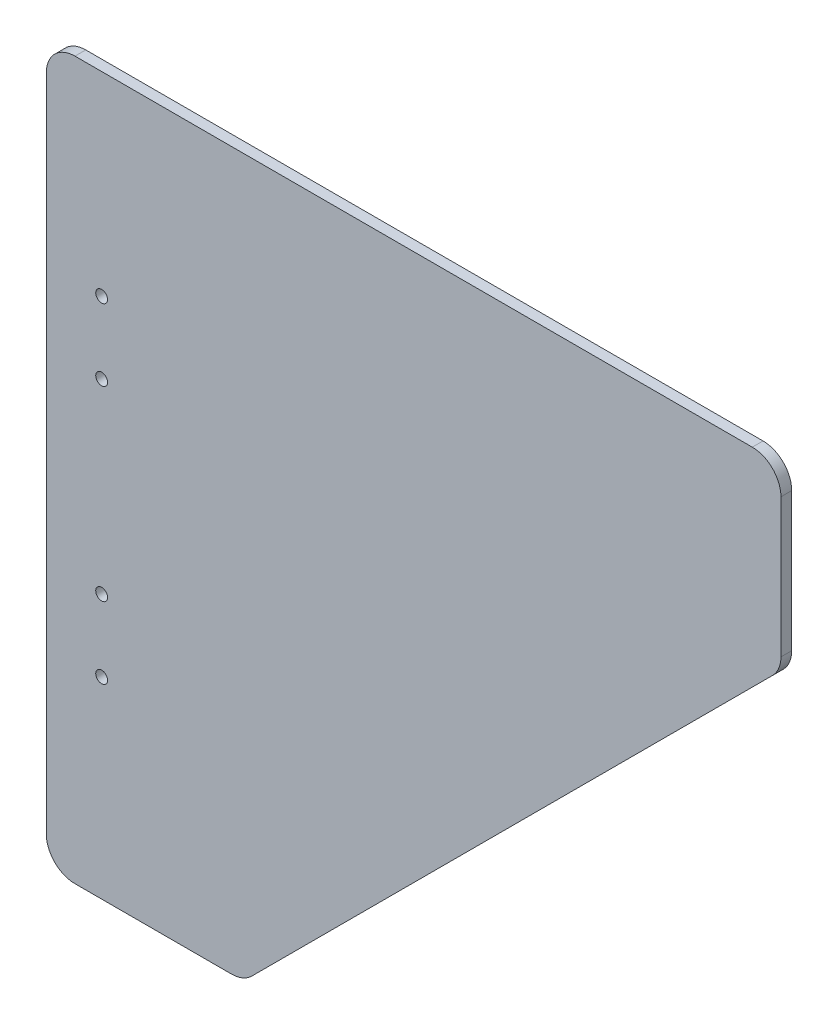
SolidWorks part; units mm, degrees
ref_plane "Piano frontale" through (0, 0, 0) normal (0, 0, 1) x (1, 0, 0)
ref_plane "Piano superiore" through (0, 0, 0) normal (0, 1, 0) x (1, 0, 0)
ref_plane "Piano destro" through (0, 0, 0) normal (1, 0, 0) x (0, 0, -1)
sketch "Schizzo1" plane through (0, 0, 0) normal (0, 0, 1) x (1, 0, 0)
  line L0 (0, 8) -> (0, 192)
  line L1 (8, 200) -> (197, 200)
  line L2 (205, 192) -> (205, 153.3137)
  line L3 (202.6569, 147.6569) -> (57.3431, 2.3431)
  line L4 (51.6863, 0) -> (8, 0)
  arc A0 (57.3431, 2.3431) -> (51.6863, 0) centre (51.6863, 8) cw
  arc A1 (205, 153.3137) -> (202.6569, 147.6569) centre (197, 153.3137) cw
  arc A2 (197, 200) -> (205, 192) centre (197, 192) cw
  arc A3 (8, 200) -> (0, 192) centre (8, 192) ccw
  arc A4 (0, 8) -> (8, 0) centre (8, 8) ccw
  point P6 (205, 172.6569)
  point P11 (205, 150)
  point P14 (205, 200)
  point P19 (0, 0)
  dimension "D5" = 8
  dimension "D6" = 8
  dimension "D1" = 45
  dimension "D2" = 50
  dimension "D3" = 200
  dimension "D4" = 205
extrude "Estrusione-Estrusione1" add sketch "Schizzo1" along normal blind 3
sketch "Schizzo2" plane through (0, 0, 3) normal (0, 0, 1) x (1, 0, 0)
  line L0 (0, 192) -> (0, 8) construction
  line L1 (8, 0) -> (51.6863, 0) construction
  line L2 (0, 100) -> (155, 100) construction
  line L3 (57.3431, 2.3431) -> (202.6569, 147.6569) construction
  circle A0 centre (16.4, 52.6) radius 2
  circle A1 centre (16.4, 72.6) radius 2
  circle A2 centre (16.4, 127.4) radius 2
  circle A3 centre (16.4, 147.4) radius 2
  dimension "D1" = 4
  dimension "D2" = 4
  dimension "D5" = 52.6
  dimension "D3" = 20
  dimension "D4" = 16.4
hole_wizard "Preforo da maschiare M4-1" positions "Schizzo3" profile "Schizzo4" hole size "M4" standard "ISO"
sketch "Schizzo3" plane through (0, 0, 3) normal (0, 0, 1) x (1, 0, 0)
  line L2 (0, 192) -> (0, 8) construction
  line L3 (197, 200) -> (8, 200) construction
  line L4 (8, 0) -> (51.6863, 0) construction
  point P0 (15.4427, 145.7)
  point P2 (15.4427, 125.7)
  point P4 (15.4427, 73.7)
  point P6 (15.4427, 53.7)
  point P14 (15.4427, 145.7)
  point P15 (0, 0)
  point P16 (0, 0)
  point P17 (15.4427, 125.7)
  point P20 (0, 0)
  point P23 (15.4427, 73.7)
  point P24 (15.4427, 53.7)
  dimension "D1" = 53.7
  dimension "D2" = 20
  dimension "D3" = 15.4427
  dimension "D4" = 20
  dimension "D5" = 54.3
sketch "Schizzo4" plane through (15.4427, 145.7, 3) normal (1, 0, 0) x (0, -1, 0)
  line L0 (0, 0) -> (0, 41.5914)
  line L1 (0, 41.5914) -> (1.65, 40.6)
  line L2 (1.65, 40.6) -> (1.65, 0)
  line L5 (1.65, 0) -> (0, 0)
  line L10 (0, 41.5914) -> (-1.65, 40.6) construction
  line L11 (0, -6.35) -> (0, 107.95) construction
  dimension "Hole Dia." = 3.3
  dimension "Hole Depth" = 40.6
  dimension "Drill Angle" = 118
